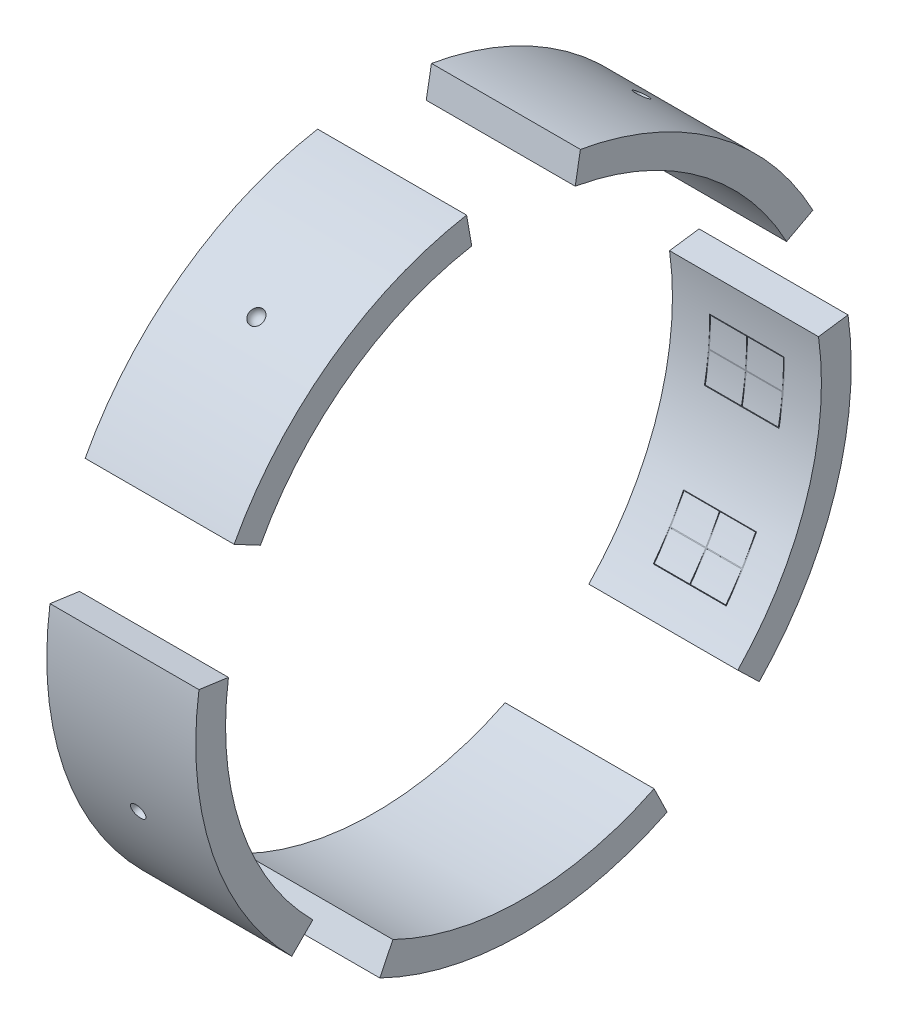
SolidWorks part; units mm, degrees
ref_plane "Front Plane" through (0, 0, 0) normal (0, 0, 1) x (1, 0, 0)
ref_plane "Top Plane" through (0, 0, 0) normal (0, 1, 0) x (1, 0, 0)
ref_plane "Right Plane" through (0, 0, 0) normal (1, 0, 0) x (0, 0, -1)
sketch "Sketch1" plane through (0, 0, 0) normal (1, 0, 0) x (0, 0, -1)
  line L1 (87.6742, -179.7588) -> (96.4417, -197.7347)
  line L2 (143.868, -138.9317) -> (158.2548, -152.8248)
  line L4 (198.0536, 27.8346) -> (217.859, 30.6181)
  line L5 (176.5895, 93.8943) -> (194.2485, 103.2837)
  line L7 (34.7296, 196.9616) -> (38.2026, 216.6577)
  line L8 (-34.7296, 196.9616) -> (-38.2026, 216.6577)
  line L10 (-176.5895, 93.8943) -> (-194.2485, 103.2837)
  line L11 (-198.0536, 27.8346) -> (-217.859, 30.6181)
  line L13 (-141.4214, -141.4214) -> (-155.5635, -155.5635)
  line L14 (-87.6742, -179.7588) -> (-96.4417, -197.7347)
  arc A0 (143.868, -138.9317) -> (198.0536, 27.8346) centre (0, 0) ccw
  arc A1 (158.2548, -152.8248) -> (217.859, 30.6181) centre (0, 0) ccw
  arc A2 (194.2485, 103.2837) -> (38.2026, 216.6577) centre (0, 0) ccw
  arc A3 (176.5895, 93.8943) -> (34.7296, 196.9616) centre (0, 0) ccw
  arc A4 (-38.2026, 216.6577) -> (-194.2485, 103.2837) centre (0, 0) ccw
  arc A5 (-34.7296, 196.9616) -> (-176.5895, 93.8943) centre (0, 0) ccw
  arc A6 (-198.0536, 27.8346) -> (-141.4214, -141.4214) centre (0, 0) ccw
  arc A7 (-217.859, 30.6181) -> (-155.5635, -155.5635) centre (0, 0) ccw
  arc A8 (-87.6742, -179.7588) -> (87.6742, -179.7588) centre (0, 0) ccw
  arc A9 (-96.4417, -197.7347) -> (96.4417, -197.7347) centre (0, 0) ccw
  point P8 (0, -220)
  point P11 (-208.6312, -69.807)
  point P14 (-129.3128, 177.9837)
  point P17 (129.3128, 177.9837)
  point P19 (209.2324, -67.9837)
  point P26 (87.6742, -179.7588)
  point P27 (143.868, -138.9317)
  point P29 (198.0536, 27.8346)
  point P30 (176.5895, 93.8943)
  point P32 (34.7296, 196.9616)
  point P33 (-34.7296, 196.9616)
extrude "Boss-Extrude1" add sketch "Sketch1" along normal blind 100
ref_plane "Plane1" through (0, 177.9837, 129.3128) normal (0, 0.809, 0.5878) x (1, 0, 0)
ref_plane "Plane2" through (0, -69.807, 208.6312) normal (0, -0.3173, 0.9483) x (1, 0, 0)
ref_plane "Plane3" through (0, -67.9837, -209.2324) normal (0, -0.309, -0.9511) x (-1, 0, 0)
ref_plane "Plane4" through (0, -220, 0) normal (0, -1, 0) x (-1, 0, 0)
ref_plane "Plane5" through (0, 177.9837, -129.3128) normal (0, 0.809, -0.5878) x (1, 0, 0)
sketch "Sketch2" plane through (0, 177.9837, 129.3128) normal (0, 0.809, 0.5878) x (1, 0, 0)
  line L0 (45, 0) -> (55, 0)
  arc A0 (55, 0) -> (45, 0) centre (50, 0) ccw
  point P6 (50, 0)
sketch "Sketch4" plane through (0, 177.9837, -129.3128) normal (0, 0.809, -0.5878) x (1, 0, 0)
  line L0 (45, 0) -> (55, 0)
  arc A0 (55, 0) -> (45, 0) centre (50, 0) ccw
  point P6 (50, 0)
sketch "Sketch5" plane through (0, -67.9837, -209.2324) normal (0, -0.309, -0.9511) x (-1, 0, 0)
  line L0 (-55, 0) -> (-45, 0)
  arc A0 (-45, 0) -> (-55, 0) centre (-50, 0) ccw
  point P5 (-50, 0)
sketch "Sketch6" plane through (0, -220, 0) normal (0, -1, 0) x (-1, 0, 0)
  line L0 (-55, 0) -> (-45, 0)
  arc A0 (-45, 0) -> (-55, 0) centre (-50, 0) cw
  point P5 (-50, 0)
sketch "Sketch7" plane through (0, -69.807, 208.6312) normal (0, -0.3173, 0.9483) x (1, 0, 0)
  line L0 (45, 0) -> (55, 0)
  arc A0 (55, 0) -> (45, 0) centre (50, 0) ccw
  point P5 (50, 0)
revolve "Cut-Revolve1" cut sketch "Sketch2" angle 360 about L0
revolve "Cut-Revolve2" cut sketch "Sketch4" angle 360 about L0
revolve "Cut-Revolve3" cut sketch "Sketch5" angle 360 about L0
revolve "Cut-Revolve4" cut sketch "Sketch6" angle 360 about L0
revolve "Cut-Revolve5" cut sketch "Sketch7" angle 360 about L0
ref_plane "Plane6" through (-10, 0, 0) normal (-1, 0, 0) x (0, 0, 1)
sketch "Sketch8" plane through (-10, 0, 0) normal (-1, 0, 0) x (0, 0, 1)
  line L0 (-129.3128, 177.9837) -> (-117.5571, 161.8034)
  line L1 (117.5571, 161.8034) -> (129.3128, 177.9837)
  line L2 (-190.2113, -61.8034) -> (-209.2324, -67.9837)
  line L3 (190.2113, -61.8034) -> (209.2324, -67.9837)
  line L4 (0, -200) -> (0, -220)
  line L5 (-150.9419, 131.2118) -> (-166.0361, 144.333)
  line L6 (-78.1462, 184.101) -> (-85.9608, 202.5111)
  line L7 (150.9419, 131.2118) -> (166.0361, 144.333)
  line L8 (78.1462, 184.101) -> (85.9608, 202.5111)
  line L9 (199.3447, -16.1766) -> (219.4045, -16.1766)
  line L10 (172.2044, -100.0777) -> (190.2113, -110.5426)
  line L11 (44.9902, -194.874) -> (49.4892, -214.3614)
  line L12 (-44.9902, -194.874) -> (-49.4892, -214.3614)
  line L13 (-171.4335, -103.0076) -> (-188.5768, -113.3084)
  line L14 (-199.2389, -17.4311) -> (-219.1628, -19.1743)
  arc A5 (-87.6742, -179.7588) -> (87.6742, -179.7588) centre (0, 0) ccw construction
  arc A6 (-198.0536, 27.8346) -> (-143.868, -138.9317) centre (0, 0) ccw construction
  arc A7 (-34.7296, 196.9616) -> (-176.5895, 93.8943) centre (0, 0) ccw construction
  arc A8 (176.5895, 93.8943) -> (34.7296, 196.9616) centre (0, 0) ccw construction
  arc A9 (141.4214, -141.4214) -> (198.0536, 27.8346) centre (0, 0) ccw construction
  circle A10 centre (0, 0) radius 220
  point P0 (-123.4349, 169.8936)
  point P1 (123.4349, 169.8936)
  point P3 (199.7219, -64.8936)
  point P5 (-117.5571, 161.8034)
  point P10 (117.5571, 161.8034)
  point P11 (190.2113, -61.8034)
  point P12 (0, -200)
  point P13 (-190.2113, -61.8034)
  point P19 (0, -210)
  point P20 (-199.7219, -64.8936)
  point P27 (-44.9902, -194.874)
  point P44 (-158.489, 137.7724)
  point P45 (-82.0535, 193.306)
  point P46 (82.0535, 193.306)
  point P47 (158.489, 137.7724)
  point P48 (209.3746, -16.1766)
  point P49 (44.9902, -194.874)
  point P53 (172.2044, -100.0777)
  point P54 (-171.4335, -103.0076)
  point P55 (-199.2389, -17.4311)
  point P59 (-150.9419, 131.2118)
  point P60 (-78.1462, 184.101)
  point P64 (78.1462, 184.101)
  point P65 (150.9419, 131.2118)
  point P69 (199.3447, -16.1766)
  point P70 (181.2078, -105.3102)
  point P74 (47.2397, -204.6177)
  point P75 (-47.2397, -204.6177)
  point P76 (-180.0051, -108.158)
  point P77 (-209.2009, -18.3027)
hole_wizard "1/2-13 Tapped Hole1" positions "3DSketch1" profile "Sketch9" tap size "1/2-13" standard "ANSI Inch"
sketch3d "3DSketch1"
  line L0 (-10, 184.101, 78.1462) -> (-10, 202.5111, 85.9608) construction
  point P0 (-10, -108.158, -180.0051)
  point P3 (-10, -18.3027, -209.2009)
  point P6 (-10, -204.6177, -47.2397)
  point P9 (-10, -204.6177, 47.2397)
  point P12 (-10, -105.3102, 181.2078)
  point P15 (-10, -16.1766, 209.3746)
  point P18 (-10, 137.7724, 158.489)
  point P21 (-10, 193.306, 82.0535)
  point P25 (-10, 137.7724, -158.489)
  point P28 (-10, 193.306, -82.0535)
sketch "Sketch9" plane through (-10, -108.158, -180.0051) normal (0, 1, 0) x (0, 0, 1)
  line L0 (0, 0) -> (0, 69.1195)
  line L1 (0, 69.1195) -> (5.3581, 65.9)
  line L2 (5.3581, 65.9) -> (5.3581, 0)
  line L5 (5.3581, 0) -> (0, 0)
  line L10 (0, 69.1195) -> (-5.3581, 65.9) construction
  line L11 (0, -6.35) -> (0, 107.95) construction
  dimension "Tap Drill Dia." = 10.7163
  dimension "Tap Drill Depth" = 65.9
  dimension "Drill Angle" = 118
ref_plane "Plane7" through (-10, -17.4311, -199.2389) normal (0, 0.0872, 0.9962) x (1, 0, 0)
sketch "Sketch10" plane through (-10, -17.4311, -199.2389) normal (0, 0.0872, 0.9962) x (1, 0, 0)
  line L0 (0, 0) -> (110, 0)
  line L1 (110, -125.8641) -> (110, 44.9902) construction
  line L2 (0, -92.0579) -> (110, -92.0579)
  line L4 (34.9502, -19.9376) -> (85.0498, -19.9376)
  line L5 (34.9502, -19.9376) -> (34.9502, 19.9376)
  line L6 (34.9502, 19.9376) -> (85.0498, 19.9376)
  line L7 (85.0498, -19.9376) -> (85.0498, 19.9376)
  line L8 (34.9502, -19.9376) -> (85.0498, 19.9376) construction
  line L9 (34.9502, 19.9376) -> (85.0498, -19.9376) construction
  line L10 (35.5, -19.5) -> (84.5, -19.5)
  line L11 (35.5, -19.5) -> (35.5, 19.5)
  line L12 (35.5, 19.5) -> (84.5, 19.5)
  line L13 (84.5, -19.5) -> (84.5, 19.5)
  line L14 (35.5, -19.5) -> (84.5, 19.5) construction
  line L15 (35.5, 19.5) -> (84.5, -19.5) construction
  point P8 (60, 0)
  point P9 (50, -92.0579)
  point P10 (60, 0)
  point P15 (60, 0)
extrude "Cut-Extrude6" cut sketch "Sketch10" along normal blind 22 contours L5 L6 L7 L4 | L11 L12 L13 L10
sketch "Sketch11" plane through (-10, -17.4311, -199.2389) normal (0, 0.0872, 0.9962) x (1, 0, 0)
  line L0 (35.5, 0.25) -> (59.75, 0.25)
  line L1 (35.5, 19.5) -> (84.5, 19.5) construction
  line L3 (60.25, -0.25) -> (60.25, -19.5)
  line L4 (84.5, -19.5) -> (84.5, 0) construction
  line L5 (60.25, 19.5) -> (60.25, 0.25)
  line L6 (35.5, -19.5) -> (84.5, -19.5) construction
  line L7 (59.75, 19.5) -> (59.75, 0.25)
  line L8 (35.5, 19.5) -> (84.5, 19.5) construction
  line L10 (35.5, 19.5) -> (35.5, 0) construction
  line L11 (84.5, 0) -> (84.5, 19.5) construction
  line L12 (84.5, -0.25) -> (60.25, -0.25)
  line L13 (35.5, -19.5) -> (35.5, 0) construction
  line L14 (60.25, 0.25) -> (84.5, 0.25)
  line L15 (59.75, -0.25) -> (59.75, -19.5)
  line L16 (59.75, -0.25) -> (35.5, -0.25)
  line L17 (84.5, 0.25) -> (84.5, -0.25)
  line L18 (60.25, 19.5) -> (59.75, 19.5)
  line L19 (35.5, 0.25) -> (35.5, -0.25)
  line L20 (59.75, -19.5) -> (60.25, -19.5)
  point P28 (60, 0)
  dimension "D3" = 0.5
extrude "Cut-Extrude7" cut sketch "Sketch11" along normal blind 28 contours L5 L14 L17 L12 L3 L20 L15 L16 L19 L0 L7 L18
ref_plane "Plane8" through (-10, -103.0076, -171.4335) normal (0, 0.515, 0.8572) x (1, 0, 0)
sketch "Sketch12" plane through (-10, -103.0076, -171.4335) normal (0, 0.515, 0.8572) x (1, 0, 0)
  line L3 (37.832, -21.6438) -> (86.7953, -21.6438)
  line L4 (37.832, -21.6438) -> (37.832, 17.1189)
  line L5 (37.832, 17.1189) -> (86.7953, 17.1189)
  line L6 (86.7953, -21.6438) -> (86.7953, 17.1189)
  line L7 (37.832, -21.6438) -> (86.7953, 17.1189) construction
  line L8 (37.832, 17.1189) -> (86.7953, -21.6438) construction
  line L9 (38.3136, -21.2625) -> (86.3136, -21.2625)
  line L10 (38.3136, -21.2625) -> (38.3136, 16.7375)
  line L11 (38.3136, 16.7375) -> (86.3136, 16.7375)
  line L12 (86.3136, -21.2625) -> (86.3136, 16.7375)
  line L13 (38.3136, -21.2625) -> (86.3136, 16.7375) construction
  line L14 (38.3136, 16.7375) -> (86.3136, -21.2625) construction
  point P1 (62.3136, -2.2625)
  point P4 (62.3136, -2.2625)
  point P9 (62.3136, -2.2625)
extrude "Cut-Extrude10" cut sketch "Sketch12" along normal blind 11 contours L4 L5 L6 L3 | L10 L11 L12 L9
ref_plane "Plane9" through (-10, -103.0076, -171.4335) normal (0, 0.515, 0.8572) x (1, 0, 0)
sketch "Sketch13" plane through (-10, -103.0076, -171.4335) normal (0, 0.515, 0.8572) x (1, 0, 0)
  line L1 (38.3136, -2.0125) -> (62.0636, -2.0125)
  line L2 (38.3136, -2.0125) -> (38.3136, -2.5125)
  line L3 (38.3136, -2.5125) -> (62.0636, -2.5125)
  line L4 (86.3136, -2.0125) -> (86.3136, -2.5125)
  line L5 (38.3136, -2.0125) -> (86.3136, -2.5125) construction
  line L6 (38.3136, -2.5125) -> (86.3136, -2.0125) construction
  line L8 (62.0636, -21.2625) -> (62.5636, -21.2625)
  line L9 (62.0636, -21.2625) -> (62.0636, -2.5125)
  line L10 (62.0636, 16.7375) -> (62.5636, 16.7375)
  line L11 (62.5636, -21.2625) -> (62.5636, -2.5125)
  line L12 (62.0636, -21.2625) -> (62.5636, 16.7375) construction
  line L13 (62.0636, 16.7375) -> (62.5636, -21.2625) construction
  line L14 (62.0636, -2.0125) -> (62.0636, 16.7375)
  line L16 (62.5636, -2.0125) -> (86.3136, -2.0125)
  line L17 (62.5636, -2.0125) -> (62.5636, 16.7375)
  line L19 (62.5636, -2.5125) -> (86.3136, -2.5125)
  point P0 (62.3136, -2.2625)
  point P8 (62.3136, -2.2625)
extrude "Cut-Extrude11" cut sketch "Sketch13" along normal blind 10
